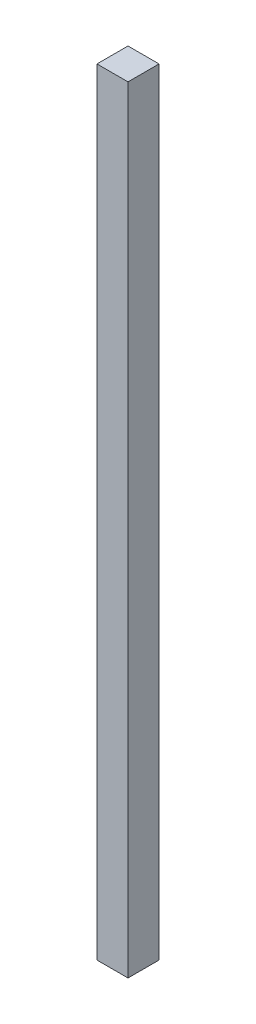
SolidWorks part; units mm, degrees
ref_plane "Front Plane" through (0, 0, 0) normal (0, 0, 1) x (1, 0, 0)
ref_plane "Top Plane" through (0, 0, 0) normal (0, 1, 0) x (1, 0, 0)
ref_plane "Right Plane" through (0, 0, 0) normal (1, 0, 0) x (0, 0, -1)
sketch "Sketch1" plane through (0, 0, 0) normal (0, 1, 0) x (1, 0, 0)
  line L1 (0, 0) -> (20, 0)
  line L2 (0, 0) -> (0, -20)
  line L3 (0, -20) -> (20, -20)
  line L4 (20, 0) -> (20, -20)
extrude "Boss-Extrude1" add sketch "Sketch1" along normal blind 500
